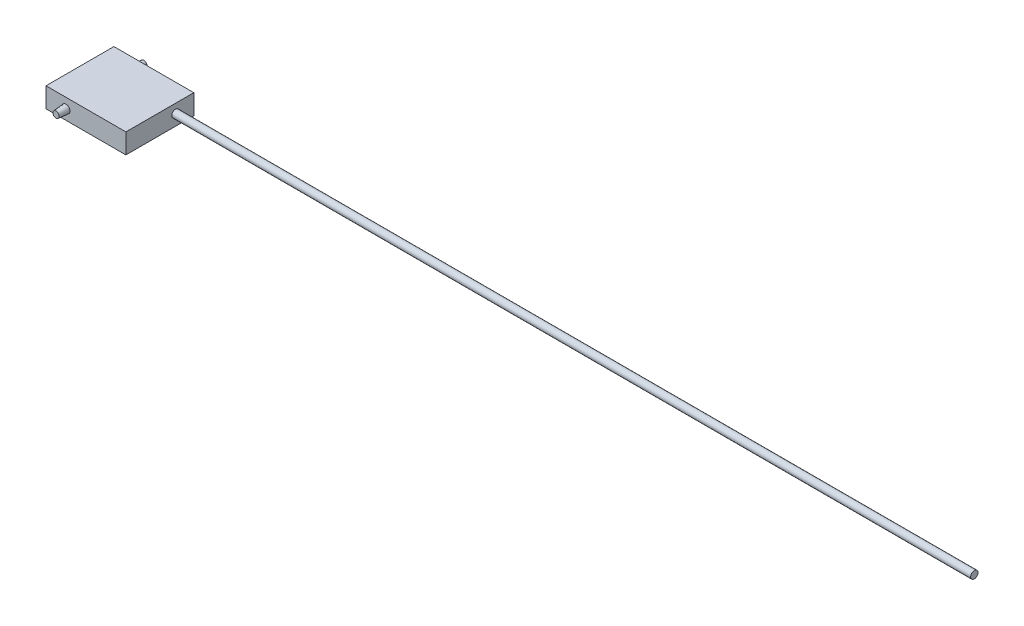
SolidWorks part; units mm, degrees
ref_plane "Front Plane" through (0, 0, 0) normal (0, 0, 1) x (1, 0, 0)
ref_plane "Top Plane" through (0, 0, 0) normal (0, 1, 0) x (1, 0, 0)
ref_plane "Right Plane" through (0, 0, 0) normal (1, 0, 0) x (0, 0, -1)
sketch "Sketch1" plane through (0, 0, 0) normal (0, 1, 0) x (1, 0, 0)
  line L1 (-12.7, -10.795) -> (12.7, -10.795)
  line L2 (-12.7, -10.795) -> (-12.7, 10.795)
  line L3 (-12.7, 10.795) -> (12.7, 10.795)
  line L4 (12.7, -10.795) -> (12.7, 10.795)
  line L5 (-12.7, -10.795) -> (12.7, 10.795) construction
  line L6 (-12.7, 10.795) -> (12.7, -10.795) construction
  point P0 (0, 0)
  dimension "D1" = 25.4
  dimension "D2" = 21.59
extrude "Boss-Extrude1" add sketch "Sketch1" along normal blind 6.35
sketch "Sketch2" plane through (0, 0, 10.795) normal (0, 0, 1) x (1, 0, 0)
  line L0 (-12.7, 6.35) -> (-12.7, 0) construction
  circle A0 centre (-6.35, 3.175) radius 1.27
  dimension "D2" = 2.54
  dimension "D1" = 6.35
extrude "Boss-Extrude2" add sketch "Sketch2" along normal blind 3.175 draft 5 contours A0
mirror "Mirror1" about plane through (0, 0, 0) normal (0, 0, 1) of "Boss-Extrude2"
sketch "Sketch3" plane through (12.7, 0, 0) normal (1, 0, 0) x (0, 0, -1)
  circle A0 centre (4.9564, 3.55) radius 1.169
extrude "Boss-Extrude3" add sketch "Sketch3" along normal blind 254
ref_plane "Plane1" through (0, 3.175, 0) normal (0, 1, 0) x (1, 0, 0)
